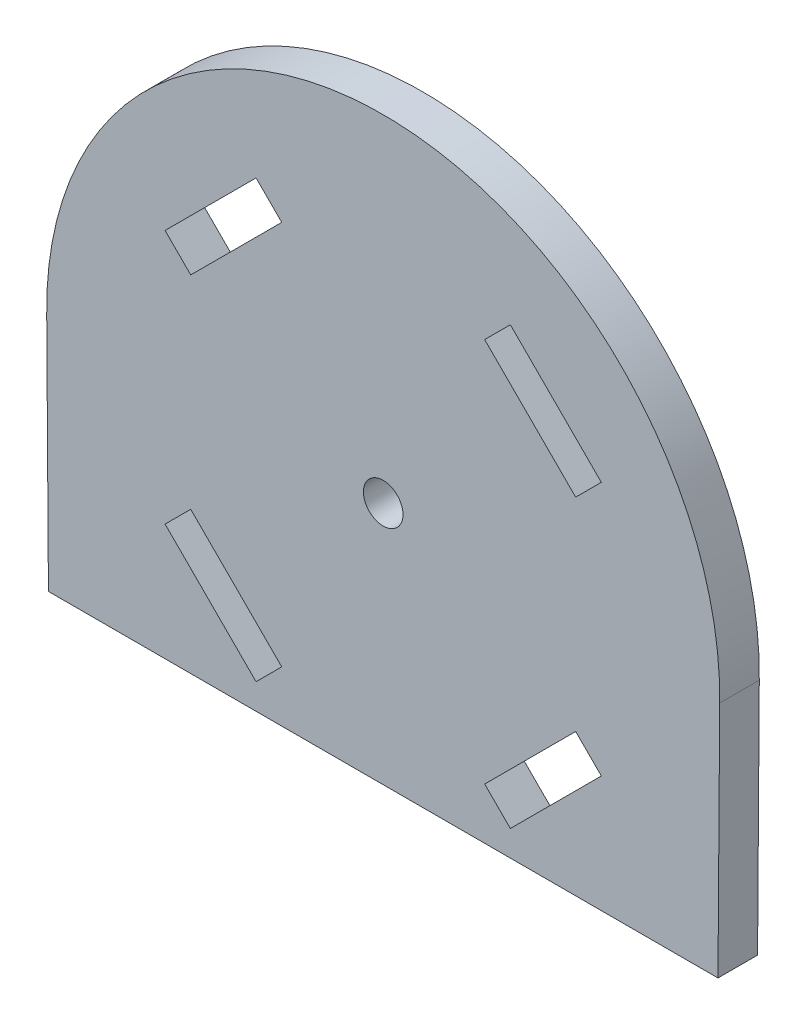
SolidWorks part; units mm, degrees
ref_plane "Front Plane" through (0, 0, 0) normal (0, 0, 1) x (1, 0, 0)
ref_plane "Top Plane" through (0, 0, 0) normal (0, 1, 0) x (1, 0, 0)
ref_plane "Right Plane" through (0, 0, 0) normal (1, 0, 0) x (0, 0, -1)
sketch "Model" plane through (0, 0, 0) normal (0, 0, 1) x (1, 0, 0)
  line L0 (49.8029, 68.0092) -> (56.6971, 74.9035)
  line L1 (56.6971, 74.9035) -> (52.8081, 78.7926)
  line L2 (52.8081, 78.7926) -> (39.0195, 65.004)
  line L3 (39.0195, 65.004) -> (42.9086, 61.1149)
  line L4 (42.9086, 61.1149) -> (49.8029, 68.0092)
  line L5 (49.8029, 68.0092) -> (42.9086, 61.1149)
  line L6 (42.9086, 61.1149) -> (39.0195, 65.004)
  line L7 (39.0195, 65.004) -> (52.8081, 78.7926)
  line L8 (52.8081, 78.7926) -> (56.6971, 74.9035)
  line L9 (56.6971, 74.9035) -> (49.8029, 68.0092)
  line L10 (49.8029, 23.4614) -> (56.6971, 16.5672)
  line L11 (56.6971, 16.5672) -> (52.8081, 12.6781)
  line L12 (52.8081, 12.6781) -> (39.0195, 26.4666)
  line L13 (39.0195, 26.4666) -> (42.9086, 30.3557)
  line L14 (42.9086, 30.3557) -> (49.8029, 23.4614)
  line L15 (49.8029, 23.4614) -> (42.9086, 30.3557)
  line L16 (42.9086, 30.3557) -> (39.0195, 26.4666)
  line L17 (39.0195, 26.4666) -> (52.8081, 12.6781)
  line L18 (52.8081, 12.6781) -> (56.6971, 16.5672)
  line L19 (56.6971, 16.5672) -> (49.8029, 23.4614)
  line L20 (94.3506, 68.0092) -> (101.2449, 61.1149)
  line L21 (101.2449, 61.1149) -> (105.134, 65.004)
  line L22 (105.134, 65.004) -> (91.3454, 78.7926)
  line L23 (91.3454, 78.7926) -> (87.4563, 74.9035)
  line L24 (87.4563, 74.9035) -> (94.3506, 68.0092)
  line L25 (94.3506, 68.0092) -> (87.4563, 74.9035)
  line L26 (87.4563, 74.9035) -> (91.3454, 78.7926)
  line L27 (91.3454, 78.7926) -> (105.134, 65.004)
  line L28 (105.134, 65.004) -> (101.2449, 61.1149)
  line L29 (101.2449, 61.1149) -> (94.3506, 68.0092)
  line L30 (94.3506, 23.4614) -> (101.2449, 30.3557)
  line L31 (101.2449, 30.3557) -> (105.134, 26.4666)
  line L32 (105.134, 26.4666) -> (91.3454, 12.6781)
  line L33 (91.3454, 12.6781) -> (87.4563, 16.5672)
  line L34 (87.4563, 16.5672) -> (94.3506, 23.4614)
  line L35 (94.3506, 23.4614) -> (87.4563, 16.5672)
  line L36 (87.4563, 16.5672) -> (91.3454, 12.6781)
  line L37 (91.3454, 12.6781) -> (105.134, 26.4666)
  line L38 (105.134, 26.4666) -> (101.2449, 30.3557)
  line L39 (101.2449, 30.3557) -> (94.3506, 23.4614)
  line L40 (39.0195, 26.4666) -> (52.8081, 12.6781)
  line L41 (122.8116, 8.789) -> (21.3418, 8.789)
  line L42 (72.0767, 8.789) -> (123.0767, 8.789)
  line L43 (21.3418, 8.789) -> (21.082, 45.0035)
  line L44 (122.8116, 8.789) -> (123.0715, 45.0035)
  arc A0 (123.0715, 45.0035) -> (21.082, 45.0035) centre (72.0767, 45.7353) ccw
  circle A1 centre (72.0767, 45.7353) radius 3
extrude "Boss-Extrude1" add sketch "Model" along normal blind 6 contours L10 L11 L12 L13 L14 | A1 | L0 L1 L2 L3 L4 | L34 L30 L31 L32 L33 | L23 L22 L21 L20 L24 | L43 A0 L44 L41
